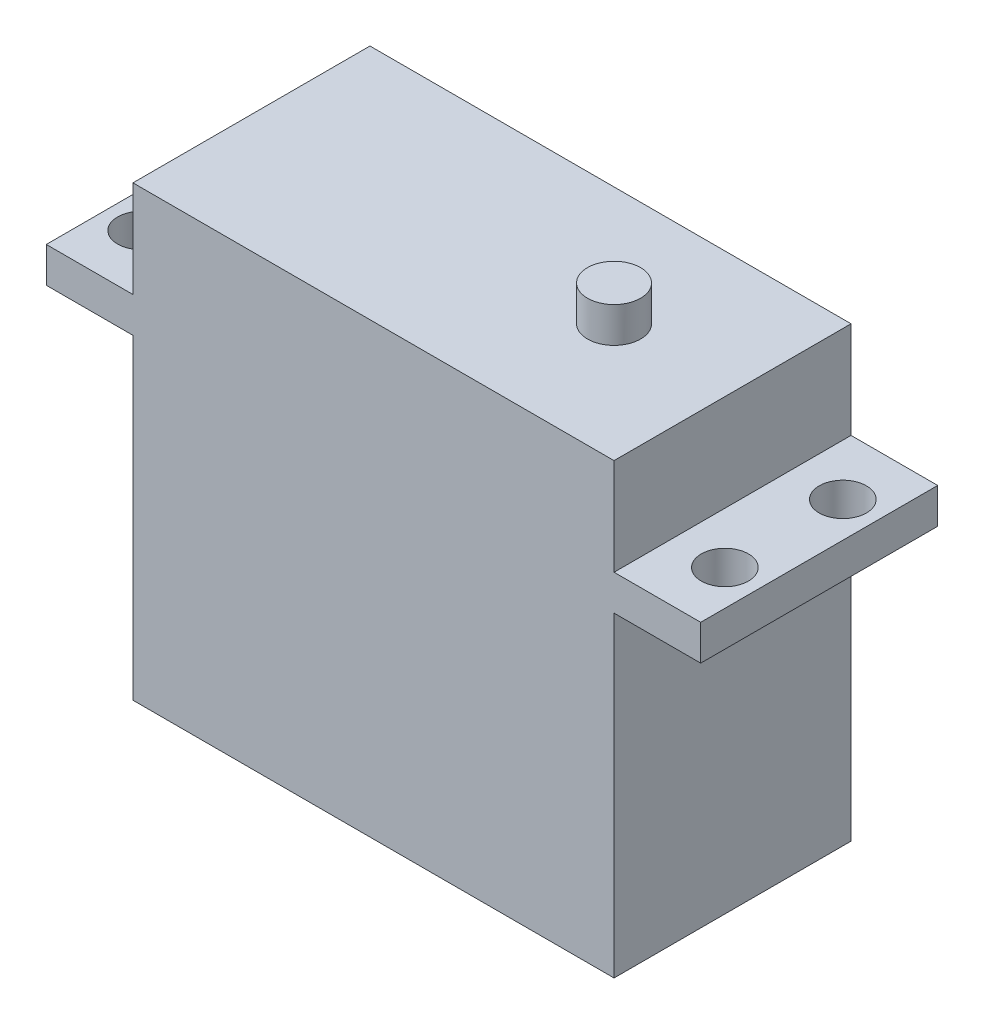
SolidWorks part; units mm, degrees
material "ABS"
ref_plane "Front Plane" through (0, 0, 0) normal (0, 0, 1) x (1, 0, 0)
ref_plane "Top Plane" through (0, 0, 0) normal (0, 1, 0) x (1, 0, 0)
ref_plane "Right Plane" through (0, 0, 0) normal (1, 0, 0) x (0, 0, -1)
sketch "Sketch1" plane through (0, 0, 0) normal (0, 0, 1) x (1, 0, 0)
  line L1 (0, 0) -> (40.8, 0)
  line L2 (0, 0) -> (0, 38)
  line L3 (0, 38) -> (40.8, 38)
  line L4 (40.8, 0) -> (40.8, 38)
  dimension "D1" = 40.8
  dimension "D2" = 38
extrude "Boss-Extrude1" add sketch "Sketch1" along normal blind 20.1
sketch "Sketch2" plane through (0, 0, 20.1) normal (0, 0, 1) x (1, 0, 0)
  line L0 (20.4, 26.8) -> (20.4, 0) construction
  line L1 (-7.35, 29.8) -> (48.15, 29.8)
  line L2 (-7.35, 29.8) -> (-7.35, 26.8)
  line L3 (-7.35, 26.8) -> (48.15, 26.8)
  line L4 (48.15, 29.8) -> (48.15, 26.8)
  line L5 (0, 0) -> (40.8, 0) construction
  dimension "D1" = 26.8
  dimension "D2" = 3
  dimension "D3" = 55.5
extrude "Boss-Extrude2" add sketch "Sketch2" against normal up to surface (20.1 mm away) up to face at (20.4, 19, 0)
sketch "Sketch3" plane through (0, 29.8, 0) normal (0, 1, 0) x (1, 0, 0)
  line L0 (-4.35, -10.05) -> (45.15, -10.05) construction
  line L1 (-4.35, -15.05) -> (45.15, -15.05) construction
  line L2 (-4.35, -15.05) -> (-4.35, -5.05) construction
  line L3 (-4.35, -5.05) -> (45.15, -5.05) construction
  line L4 (45.15, -15.05) -> (45.15, -5.05) construction
  line L6 (0, -20.1) -> (0, 0) construction
  line L7 (40.8, 0) -> (0, 0) construction
  circle A0 centre (-4.35, -5.05) radius 2
  circle A1 centre (-4.35, -15.05) radius 2
  circle A2 centre (45.15, -15.05) radius 2
  circle A3 centre (45.15, -5.05) radius 2
  point P14 (0, -10.05)
  point P15 (20.4, 0)
  point P16 (20.4, -10.05)
  dimension "D1" = 4
  dimension "D2" = 49.5
  dimension "D3" = 10
extrude "Cut-Extrude1" cut sketch "Sketch3" against normal through all
sketch "Sketch4" plane through (0, 38, 0) normal (0, 1, 0) x (1, 0, 0)
  line L0 (40.8, -20.1) -> (40.8, 0) construction
  line L1 (40.8, 0) -> (0, 0) construction
  line L2 (40.8, -20.1) -> (0, -20.1) construction
  circle A0 centre (30.75, -10.05) radius 10.05 construction
  circle A1 centre (30.75, -10.05) radius 2.25
  point P10 (0, 0)
  dimension "D1" = 4.5
extrude "Boss-Extrude3" add sketch "Sketch4" along normal blind 3
